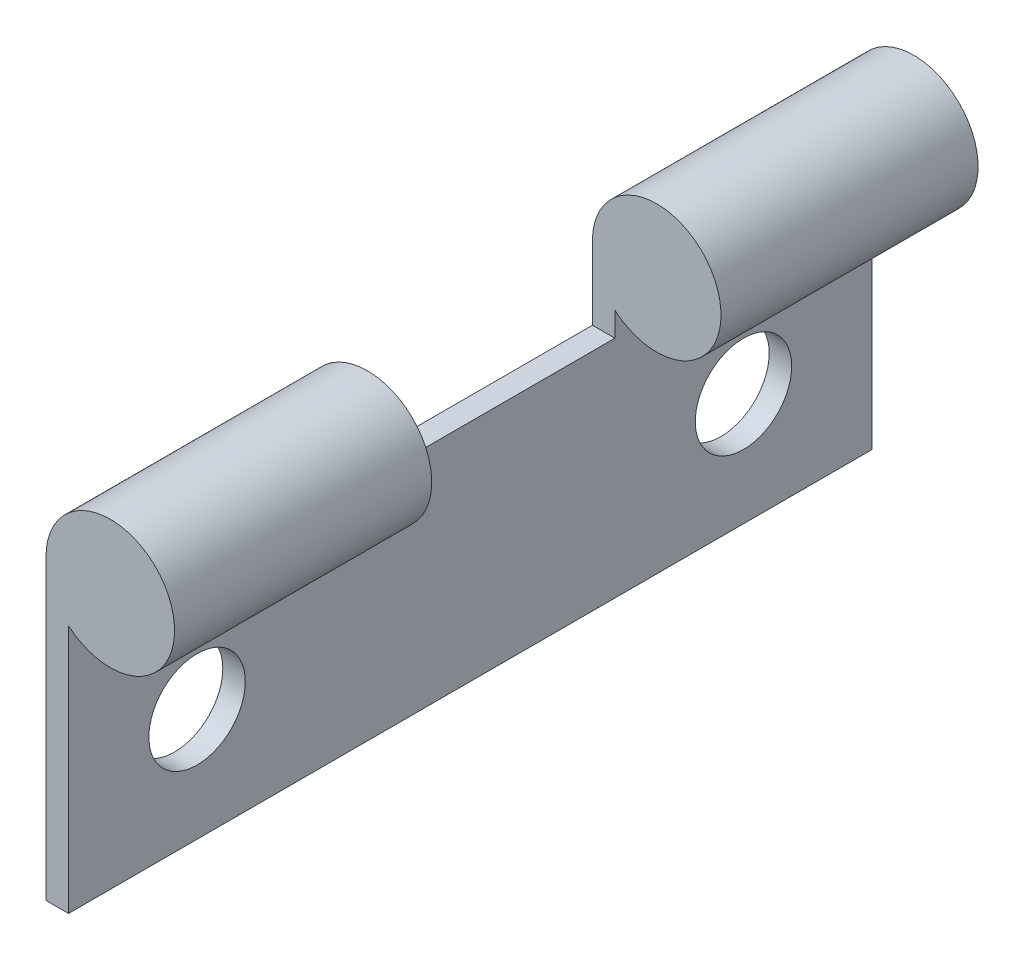
SolidWorks part; units mm, degrees
ref_plane "前视基准面" through (0, 0, 0) normal (0, 0, 1) x (1, 0, 0)
ref_plane "上视基准面" through (0, 0, 0) normal (0, 1, 0) x (1, 0, 0)
ref_plane "右视基准面" through (0, 0, 0) normal (1, 0, 0) x (0, 0, -1)
other "Configuration Table"
sketch "草图1" plane through (0, 0, 0) normal (1, 0, 0) x (0, 0, -1)
  line L2 (185.9638, 67.5747) -> (185.9638, 60.5747)
  line L3 (185.9638, 60.5747) -> (160.9638, 60.5747)
  line L4 (160.9638, 67.5747) -> (160.9638, 60.5747)
  line L9 (160.9638, 67.5747) -> (160.9638, 69.8483)
  line L10 (160.9638, 69.8483) -> (168.9638, 69.8483)
  line L11 (177.9638, 69.8483) -> (185.9638, 69.8483)
  line L12 (185.9638, 69.8483) -> (185.9638, 67.5747)
  line L13 (168.9638, 67.5747) -> (168.9638, 69.8483)
  line L14 (177.9638, 69.8483) -> (177.9638, 67.5747)
  line L15 (168.9638, 67.5747) -> (177.9638, 67.5747)
  circle A0 centre (181.9638, 64.0747) radius 1.5
  circle A1 centre (164.9638, 64.0747) radius 1.5
  dimension "D5" = 3
  dimension "D6" = 3
  dimension "D1" = 25
  dimension "D2" = 7
  dimension "D3" = 9
  dimension "D4" = 8
  dimension "D7" = 3.5
  dimension "D8" = 3.5
  dimension "D9" = 17
  dimension "D10" = 4
extrude "凸台-拉伸1" add sketch "草图1" along normal blind 0.7 contours L4 L3 L2 L12 L11 L14 L15 L13 L10 L9 | A0 | A1
ref_plane "基准面1" through (0, 0, -173.4638) normal (0, 0, 1) x (1, 0, 0)
sketch "草图3" plane through (0, 0, -160.9638) normal (0, 0, 1) x (1, 0, 0)
  circle A0 centre (2, 69.8483) radius 2
  dimension "D1" = 4
extrude "凸台-拉伸3" add sketch "草图3" against normal up to surface (8 mm away) up to face at (0.35, 68.7115, -168.9638)
sketch "草图4" plane through (0, 0, -185.9638) normal (0, 0, -1) x (-1, 0, 0)
  circle A0 centre (-2, 69.8483) radius 2
extrude "凸台-拉伸4" add sketch "草图4" against normal up to surface (8 mm away) up to face at (0.35, 68.7115, -177.9638)
